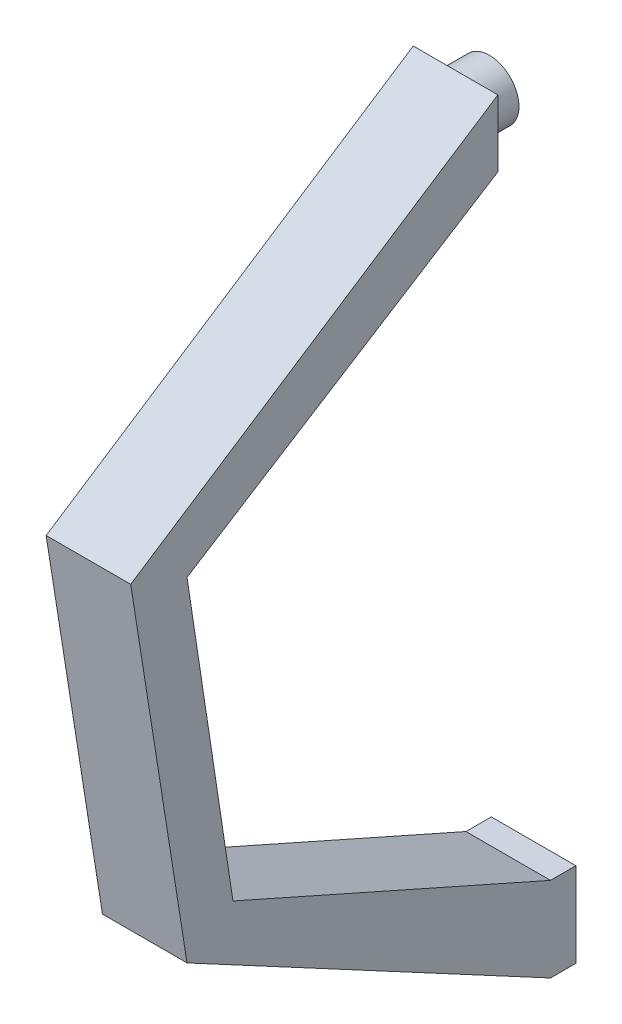
SolidWorks part; units mm, degrees
ref_plane "Front Plane" through (0, 0, 0) normal (0, 0, 1) x (1, 0, 0)
ref_plane "Top Plane" through (0, 0, 0) normal (0, 1, 0) x (1, 0, 0)
ref_plane "Right Plane" through (0, 0, 0) normal (1, 0, 0) x (0, 0, -1)
sketch "Sketch1" plane through (0, 0, 0) normal (0, 0, 1) x (1, 0, 0)
  line L0 (0, 0) -> (100, 0)
  line L1 (100, 0) -> (100, 100)
  line L2 (100, 100) -> (0, 100)
  line L3 (0, 100) -> (0, 0)
  dimension "D1" = 100
  dimension "D2" = 100
extrude "Boss-Extrude1" add sketch "Sketch1" along normal blind 30
sketch "Sketch2" plane through (0, 0, 0) normal (1, 0, 0) x (0, 0, -1)
  line L0 (-30, 100) -> (-405.5457, 266.6517)
  line L1 (-405.5457, 266.6517) -> (-459.8438, 625.256)
  line L2 (-459.8438, 625.256) -> (-92.2903, 856.6697)
  line L3 (-92.2903, 856.6697) -> (-92.2903, 935.6226)
  line L4 (-92.2903, 935.6226) -> (-526.4358, 651.4221)
  line L5 (-526.4358, 651.4221) -> (-459.8438, 230.3559)
  line L6 (-30, 100) -> (-30, 0)
  line L7 (-30, 0) -> (-459.8438, 230.3559)
  point P9 (-160.3531, 851.2247)
  point P10 (-160.3531, 919.2875)
  point P12 (-92.2903, 804.9419)
  point P13 (-92.2903, 1006.4079)
  point P14 (-92.2903, 911.12)
  point P15 (-92.2903, 935.6226)
  point P16 (0, 0)
  point P17 (-92.2903, 856.6697)
  point P18 (0, 0)
  point P19 (0, 0)
  point P20 (-459.8438, 625.256)
extrude "Boss-Extrude2" add sketch "Sketch2" along normal blind 100 contours L1 L2 L3 L4 L5 L7 L6 L0
ref_plane "Plane1" through (0, 0, 92.2903) normal (0, 0, -1) x (-1, 0, 0)
sketch "Sketch4" plane through (0, 0, 92.2903) normal (0, 0, -1) x (-1, 0, 0)
  line L0 (-50, 935.6226) -> (-50, 856.6697)
  line L1 (-100, 935.6226) -> (0, 935.6226) construction
  line L2 (-100, 856.6697) -> (0, 856.6697) construction
  circle A0 centre (-50, 896.1461) radius 35
extrude "Boss-Extrude3" add sketch "Sketch4" along normal blind 40 contours A0
